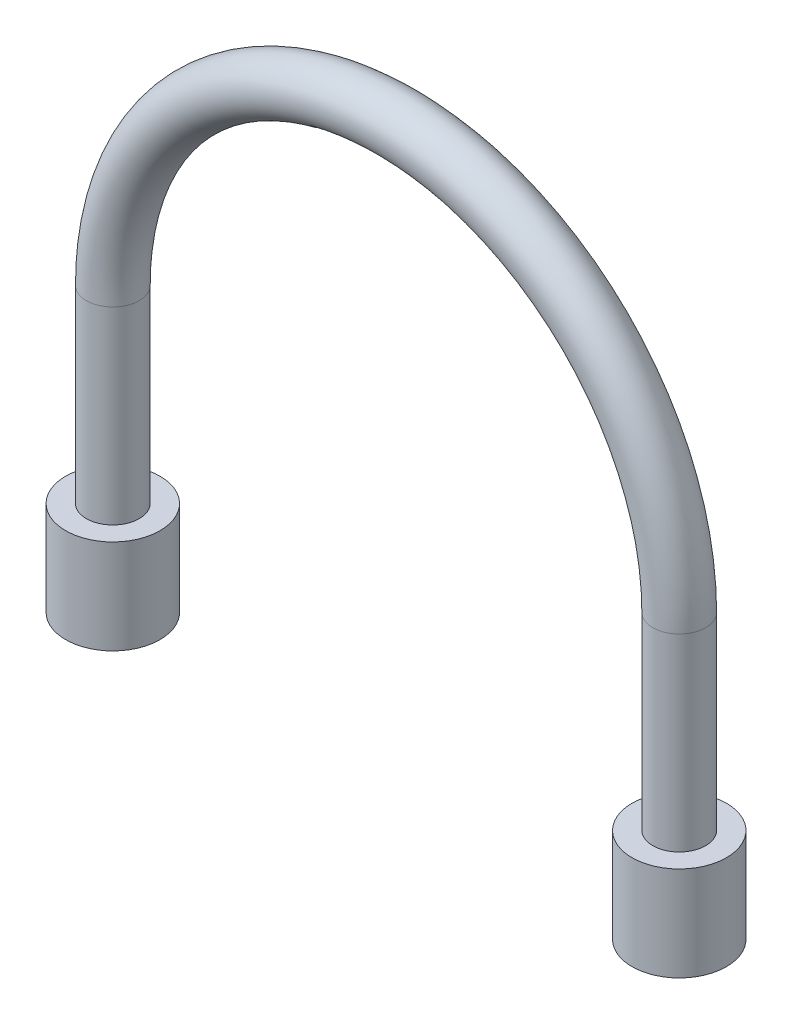
SolidWorks part; units mm, degrees
material "AISI 304"
ref_plane "Front Plane" through (0, 0, 0) normal (0, 0, 1) x (1, 0, 0)
ref_plane "Top Plane" through (0, 0, 0) normal (0, 1, 0) x (1, 0, 0)
ref_plane "Right Plane" through (0, 0, 0) normal (1, 0, 0) x (0, 0, -1)
sketch "Sketch2" plane through (0, 0, 0) normal (0, 0, 1) x (1, 0, 0)
  line L0 (-19.05, 0) -> (-19.05, 12.7)
  line L1 (19.05, 0) -> (19.05, 12.7)
  arc A0 (-19.05, 12.7) -> (19.05, 12.7) centre (0, 12.7) cw
  dimension "D1" = 19.05
  dimension "D2" = 19.05
  dimension "D3" = 12.7
  dimension "D4" = 12.7
ref_plane "Plane1" through (0, 0, 0) normal (0, 1, 0) x (1, 0, 0)
sketch "Sketch3" plane through (0, 0, 0) normal (0, 1, 0) x (1, 0, 0)
  circle A0 centre (-19.05, 0) radius 1.778
  dimension "D1" = 3.556
sweep "Sweep1" add profiles "Sketch3" path "Sketch2"
sketch "Sketch4" plane through (0, 0, 0) normal (0, -1, 0) x (1, 0, 0)
  circle A0 centre (-19.05, 0) radius 3.175
  dimension "D1" = 6.35
extrude "Boss-Extrude1" add sketch "Sketch4" along normal blind 6.35
sketch "Sketch5" plane through (0, 0, 0) normal (0, -1, 0) x (1, 0, 0)
  circle A0 centre (19.05, 0) radius 3.175
  dimension "D1" = 6.35
extrude "Boss-Extrude2" add sketch "Sketch5" along normal blind 6.35
ref_plane "Plane2" through (0, 27.94, 0) normal (0, 1, 0) x (1, 0, 0)
sketch "Sketch6" plane through (0, 27.94, 0) normal (0, 1, 0) x (1, 0, 0)
  line L1 (4.4477, 1.293) -> (-4.4477, 1.293)
  line L2 (4.4477, 1.293) -> (4.4477, -1.293)
  line L3 (4.4477, -1.293) -> (-4.4477, -1.293)
  line L4 (-4.4477, 1.293) -> (-4.4477, -1.293)
  line L5 (4.4477, 1.293) -> (-4.4477, -1.293) construction
  line L6 (4.4477, -1.293) -> (-4.4477, 1.293) construction
  point P0 (0, 0)
extrude "Cut-Extrude1" cut sketch "Sketch6" along normal blind 2.54
